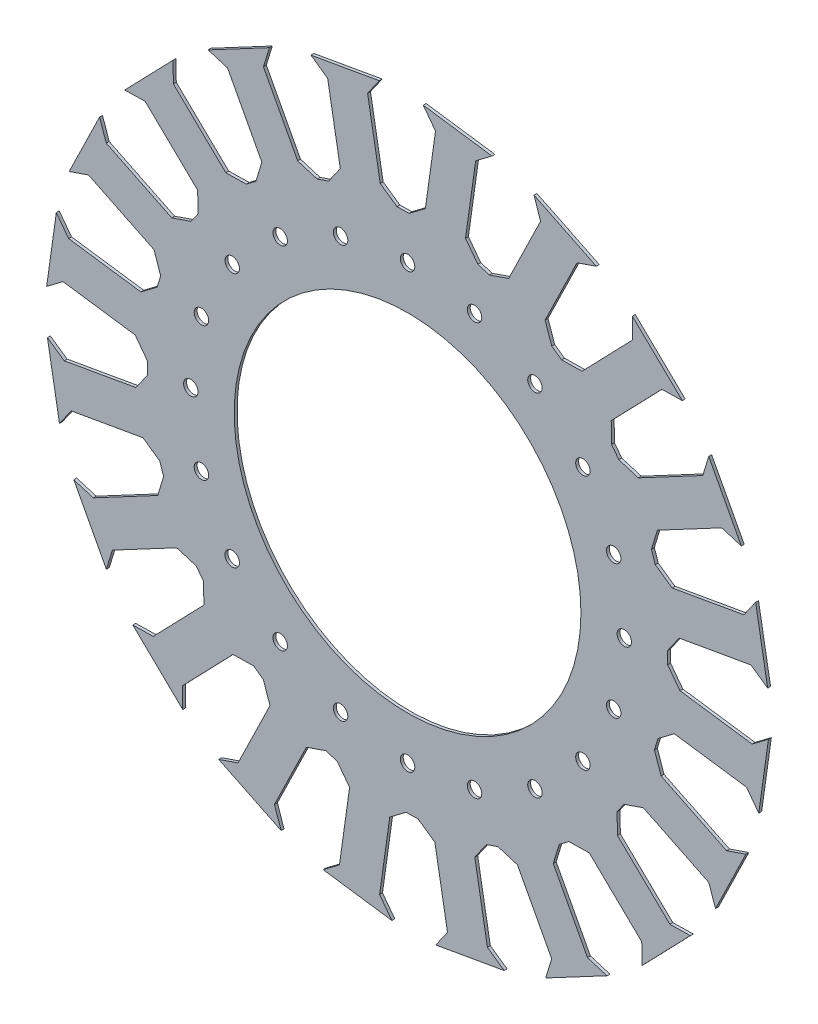
SolidWorks part; units mm, degrees
ref_plane "Ön Düzlem" through (0, 0, 0) normal (0, 0, 1) x (1, 0, 0)
ref_plane "Üst Düzlem" through (0, 0, 0) normal (0, 1, 0) x (1, 0, 0)
ref_plane "Sağ Düzlem" through (0, 0, 0) normal (1, 0, 0) x (0, 0, -1)
sketch "Çizim1" plane through (0, 0, 0) normal (0, 0, 1) x (1, 0, 0)
  line L0 (-3.656, 89.9257) -> (-1.5703, 89.9621)
  line L1 (-27.3209, 85.7529) -> (-29.2933, 85.0738)
  line L2 (-33.438, 120.4446) -> (-9.773, 124.6174)
  line L3 (-9.4482, 93.9815) -> (-13.8288, 118.8251)
  line L4 (-31.2656, 84.3947) -> (-29.2933, 85.0738)
  line L5 (-52.4829, 73.1133) -> (-54.1488, 71.8579)
  line L6 (-69.0208, 104.2167) -> (-47.8036, 115.4981)
  line L7 (-23.2651, 91.5452) -> (-27.6457, 116.3888)
  line L8 (-9.773, 124.6174) -> (-13.8288, 118.8251)
  line L9 (-33.438, 120.4446) -> (-27.6457, 116.3888)
  line L10 (-23.2651, 91.5452) -> (-27.3209, 85.7529)
  line L11 (-9.4482, 93.9815) -> (-3.656, 89.9257)
  line L12 (24.3115, 86.6542) -> (26.3064, 86.0443)
  line L13 (0.5154, 89.9985) -> (-1.5703, 89.9621)
  line L14 (5.418, 124.8825) -> (29.2142, 121.5382)
  line L15 (20.0561, 92.3014) -> (23.567, 117.2827)
  line L16 (6.1626, 94.254) -> (9.6735, 119.2353)
  line L17 (29.2142, 121.5382) -> (23.567, 117.2827)
  line L18 (5.418, 124.8825) -> (9.6735, 119.2353)
  line L19 (6.1626, 94.254) -> (0.5154, 89.9985)
  line L20 (20.0561, 92.3014) -> (24.3115, 86.6542)
  line L21 (49.8993, 74.9004) -> (51.608, 73.7039)
  line L22 (28.3012, 85.4344) -> (26.3064, 86.0443)
  line L23 (43.7437, 117.0961) -> (65.3417, 106.562)
  line L24 (47.5972, 81.5862) -> (58.6559, 104.2599)
  line L25 (34.9871, 87.7365) -> (46.0458, 110.4103)
  line L26 (65.3417, 106.562) -> (58.6559, 104.2599)
  line L27 (43.7437, 117.0961) -> (46.0458, 110.4103)
  line L28 (34.9871, 87.7365) -> (28.3012, 85.4344)
  line L29 (47.5972, 81.5862) -> (49.8993, 74.9004)
  line L30 (70.6025, 55.8147) -> (71.8579, 54.1488)
  line L31 (53.3168, 72.5074) -> (51.608, 73.7039)
  line L32 (77.7874, 97.8475) -> (95.0731, 81.1548)
  line L33 (70.4791, 62.8847) -> (88.0031, 81.0314)
  line L34 (60.3867, 72.6308) -> (77.9108, 90.7775)
  line L35 (95.0731, 81.1548) -> (88.0031, 81.0314)
  line L36 (77.7874, 97.8475) -> (77.9108, 90.7775)
  line L37 (60.3867, 72.6308) -> (53.3168, 72.5074)
  line L38 (70.4791, 62.8847) -> (70.6025, 55.8147)
  line L39 (84.3947, 31.2656) -> (85.0738, 29.2933)
  line L40 (73.1133, 52.4829) -> (71.8579, 54.1488)
  line L41 (104.2167, 69.0208) -> (115.4981, 47.8036)
  line L42 (86.4621, 38.0277) -> (108.736, 49.871)
  line L43 (79.8754, 50.4155) -> (102.1493, 62.2588)
  line L44 (115.4981, 47.8036) -> (108.736, 49.871)
  line L45 (104.2167, 69.0208) -> (102.1493, 62.2588)
  line L46 (79.8754, 50.4155) -> (73.1133, 52.4829)
  line L47 (86.4621, 38.0277) -> (84.3947, 31.2656)
  line L48 (89.9257, 3.656) -> (89.9621, 1.5703)
  line L49 (85.7529, 27.3209) -> (85.0738, 29.2933)
  line L50 (120.4446, 33.438) -> (124.6174, 9.773)
  line L51 (93.9815, 9.4482) -> (118.8251, 13.8288)
  line L52 (91.5452, 23.2651) -> (116.3888, 27.6457)
  line L53 (124.6174, 9.773) -> (118.8251, 13.8288)
  line L54 (120.4446, 33.438) -> (116.3888, 27.6457)
  line L55 (91.5452, 23.2651) -> (85.7529, 27.3209)
  line L56 (93.9815, 9.4482) -> (89.9257, 3.656)
  line L57 (86.6542, -24.3115) -> (86.0443, -26.3064)
  line L58 (89.9985, -0.5154) -> (89.9621, 1.5703)
  line L59 (124.8825, -5.418) -> (121.5382, -29.2142)
  line L60 (92.3014, -20.0561) -> (117.2827, -23.567)
  line L61 (94.254, -6.1626) -> (119.2353, -9.6735)
  line L62 (121.5382, -29.2142) -> (117.2827, -23.567)
  line L63 (124.8825, -5.418) -> (119.2353, -9.6735)
  line L64 (94.254, -6.1626) -> (89.9985, -0.5154)
  line L65 (92.3014, -20.0561) -> (86.6542, -24.3115)
  line L66 (74.9004, -49.8993) -> (73.7039, -51.608)
  line L67 (85.4344, -28.3012) -> (86.0443, -26.3064)
  line L68 (117.0961, -43.7437) -> (106.562, -65.3417)
  line L69 (81.5862, -47.5972) -> (104.2599, -58.6559)
  line L70 (87.7365, -34.9871) -> (110.4103, -46.0458)
  line L71 (106.562, -65.3417) -> (104.2599, -58.6559)
  line L72 (117.0961, -43.7437) -> (110.4103, -46.0458)
  line L73 (87.7365, -34.9871) -> (85.4344, -28.3012)
  line L74 (81.5862, -47.5972) -> (74.9004, -49.8993)
  line L75 (55.8147, -70.6025) -> (54.1488, -71.8579)
  line L76 (72.5074, -53.3168) -> (73.7039, -51.608)
  line L77 (97.8475, -77.7874) -> (81.1548, -95.0731)
  line L78 (62.8847, -70.4791) -> (81.0314, -88.0031)
  line L79 (72.6308, -60.3867) -> (90.7775, -77.9108)
  line L80 (-38.0277, 86.4621) -> (-49.871, 108.736)
  line L81 (81.1548, -95.0731) -> (81.0314, -88.0031)
  line L82 (-50.4155, 79.8754) -> (-62.2588, 102.1493)
  line L83 (97.8475, -77.7874) -> (90.7775, -77.9108)
  line L84 (-47.8036, 115.4981) -> (-49.871, 108.736)
  line L85 (-69.0208, 104.2167) -> (-62.2588, 102.1493)
  line L86 (-50.4155, 79.8754) -> (-52.4829, 73.1133)
  line L87 (-38.0277, 86.4621) -> (-31.2656, 84.3947)
  line L88 (72.6308, -60.3867) -> (72.5074, -53.3168)
  line L90 (-52.4829, 73.1133) -> (-69.0208, 104.2167) construction
  line L92 (-31.2656, 84.3947) -> (-47.8036, 115.4981) construction
  line L93 (-62.2588, 102.1493) -> (-49.871, 108.736) construction
  line L94 (-38.0277, 86.4621) -> (-50.4155, 79.8754) construction
  line L96 (-31.2656, 84.3947) -> (-52.4829, 73.1133) construction
  line L105 (62.8847, -70.4791) -> (55.8147, -70.6025)
  line L106 (31.2656, -84.3947) -> (29.2933, -85.0738)
  line L107 (52.4829, -73.1133) -> (54.1488, -71.8579)
  line L108 (69.0208, -104.2167) -> (47.8036, -115.4981)
  line L109 (38.0277, -86.4621) -> (49.871, -108.736)
  line L110 (50.4155, -79.8754) -> (62.2588, -102.1493)
  line L111 (47.8036, -115.4981) -> (49.871, -108.736)
  line L112 (69.0208, -104.2167) -> (62.2588, -102.1493)
  line L113 (50.4155, -79.8754) -> (52.4829, -73.1133)
  line L114 (38.0277, -86.4621) -> (31.2656, -84.3947)
  line L115 (3.656, -89.9257) -> (1.5703, -89.9621)
  line L116 (27.3209, -85.7529) -> (29.2933, -85.0738)
  line L117 (33.438, -120.4446) -> (9.773, -124.6174)
  line L118 (9.4482, -93.9815) -> (13.8288, -118.8251)
  line L119 (23.2651, -91.5452) -> (27.6457, -116.3888)
  line L120 (9.773, -124.6174) -> (13.8288, -118.8251)
  line L121 (33.438, -120.4446) -> (27.6457, -116.3888)
  line L122 (23.2651, -91.5452) -> (27.3209, -85.7529)
  line L123 (9.4482, -93.9815) -> (3.656, -89.9257)
  line L124 (-24.3115, -86.6542) -> (-26.3064, -86.0443)
  line L125 (-0.5154, -89.9985) -> (1.5703, -89.9621)
  line L126 (-5.418, -124.8825) -> (-29.2142, -121.5382)
  line L127 (-20.0561, -92.3014) -> (-23.567, -117.2827)
  line L128 (-6.1626, -94.254) -> (-9.6735, -119.2353)
  line L129 (-29.2142, -121.5382) -> (-23.567, -117.2827)
  line L130 (-5.418, -124.8825) -> (-9.6735, -119.2353)
  line L131 (-6.1626, -94.254) -> (-0.5154, -89.9985)
  line L132 (-20.0561, -92.3014) -> (-24.3115, -86.6542)
  line L133 (-49.8993, -74.9004) -> (-51.608, -73.7039)
  line L134 (-28.3012, -85.4344) -> (-26.3064, -86.0443)
  line L135 (-43.7437, -117.0961) -> (-65.3417, -106.562)
  line L136 (-47.5972, -81.5862) -> (-58.6559, -104.2599)
  line L137 (-34.9871, -87.7365) -> (-46.0458, -110.4103)
  line L138 (-65.3417, -106.562) -> (-58.6559, -104.2599)
  line L139 (-43.7437, -117.0961) -> (-46.0458, -110.4103)
  line L140 (-34.9871, -87.7365) -> (-28.3012, -85.4344)
  line L141 (-47.5972, -81.5862) -> (-49.8993, -74.9004)
  line L142 (-70.6025, -55.8147) -> (-71.8579, -54.1488)
  line L143 (-53.3168, -72.5074) -> (-51.608, -73.7039)
  line L144 (-77.7874, -97.8475) -> (-95.0731, -81.1548)
  line L145 (-70.4791, -62.8847) -> (-88.0031, -81.0314)
  line L146 (-60.3867, -72.6308) -> (-77.9108, -90.7775)
  line L147 (-95.0731, -81.1548) -> (-88.0031, -81.0314)
  line L148 (-77.7874, -97.8475) -> (-77.9108, -90.7775)
  line L149 (-60.3867, -72.6308) -> (-53.3168, -72.5074)
  line L150 (-70.4791, -62.8847) -> (-70.6025, -55.8147)
  line L151 (-84.3947, -31.2656) -> (-85.0738, -29.2933)
  line L152 (-73.1133, -52.4829) -> (-71.8579, -54.1488)
  line L153 (-104.2167, -69.0208) -> (-115.4981, -47.8036)
  line L154 (-86.4621, -38.0277) -> (-108.736, -49.871)
  line L155 (-79.8754, -50.4155) -> (-102.1493, -62.2588)
  line L156 (-115.4981, -47.8036) -> (-108.736, -49.871)
  line L157 (-104.2167, -69.0208) -> (-102.1493, -62.2588)
  line L158 (-79.8754, -50.4155) -> (-73.1133, -52.4829)
  line L159 (-86.4621, -38.0277) -> (-84.3947, -31.2656)
  line L160 (-89.9257, -3.656) -> (-89.9621, -1.5703)
  line L161 (-85.7529, -27.3209) -> (-85.0738, -29.2933)
  line L162 (-120.4446, -33.438) -> (-124.6174, -9.773)
  line L163 (-93.9815, -9.4482) -> (-118.8251, -13.8288)
  line L164 (-91.5452, -23.2651) -> (-116.3888, -27.6457)
  line L165 (-124.6174, -9.773) -> (-118.8251, -13.8288)
  line L166 (-120.4446, -33.438) -> (-116.3888, -27.6457)
  line L167 (-91.5452, -23.2651) -> (-85.7529, -27.3209)
  line L168 (-93.9815, -9.4482) -> (-89.9257, -3.656)
  line L169 (-86.6542, 24.3115) -> (-86.0443, 26.3064)
  line L170 (-89.9985, 0.5154) -> (-89.9621, -1.5703)
  line L171 (-124.8825, 5.418) -> (-121.5382, 29.2142)
  line L172 (-92.3014, 20.0561) -> (-117.2827, 23.567)
  line L173 (-94.254, 6.1626) -> (-119.2353, 9.6735)
  line L174 (-121.5382, 29.2142) -> (-117.2827, 23.567)
  line L175 (-124.8825, 5.418) -> (-119.2353, 9.6735)
  line L176 (-94.254, 6.1626) -> (-89.9985, 0.5154)
  line L177 (-92.3014, 20.0561) -> (-86.6542, 24.3115)
  line L178 (-74.9004, 49.8993) -> (-73.7039, 51.608)
  line L179 (-85.4344, 28.3012) -> (-86.0443, 26.3064)
  line L180 (-117.0961, 43.7437) -> (-106.562, 65.3417)
  line L181 (-81.5862, 47.5972) -> (-104.2599, 58.6559)
  line L182 (-87.7365, 34.9871) -> (-110.4103, 46.0458)
  line L183 (-106.562, 65.3417) -> (-104.2599, 58.6559)
  line L184 (-117.0961, 43.7437) -> (-110.4103, 46.0458)
  line L185 (-87.7365, 34.9871) -> (-85.4344, 28.3012)
  line L186 (-81.5862, 47.5972) -> (-74.9004, 49.8993)
  line L187 (-55.8147, 70.6025) -> (-54.1488, 71.8579)
  line L188 (-72.5074, 53.3168) -> (-73.7039, 51.608)
  line L189 (-97.8475, 77.7874) -> (-81.1548, 95.0731)
  line L190 (-62.8847, 70.4791) -> (-81.0314, 88.0031)
  line L191 (-72.6308, 60.3867) -> (-90.7775, 77.9108)
  line L192 (-81.1548, 95.0731) -> (-81.0314, 88.0031)
  line L193 (-97.8475, 77.7874) -> (-90.7775, 77.9108)
  line L194 (-72.6308, 60.3867) -> (-72.5074, 53.3168)
  line L195 (-62.8847, 70.4791) -> (-55.8147, 70.6025)
  point P82 (0, 0)
  point P226 (0, 0)
  dimension "D1" = 20
  dimension "D2" = 5
extrude "Yükseklik-Ekstrüzyon1" add sketch "Çizim1" along normal blind 1
sketch "Çizim2" plane through (0, 0, 1) normal (0, 0, 1) x (1, 0, 0)
  circle A0 centre (0, 0) radius 60
extrude "Kes-Ekstrüzyon1" cut sketch "Çizim2" against normal blind 1
sketch "Çizim3" plane through (0, 0, 1) normal (0, 0, 1) x (1, 0, 0)
  circle A0 centre (37.5, 64.9519) radius 2.5
  circle A1 centre (0, 75) radius 2.5
  circle A2 centre (64.9519, 37.5) radius 2.5
  circle A3 centre (75, 0) radius 2.5
  circle A4 centre (64.9519, -37.5) radius 2.5
  circle A5 centre (37.5, -64.9519) radius 2.5
  circle A6 centre (0, -75) radius 2.5
  circle A7 centre (-37.5, -64.9519) radius 2.5
  circle A8 centre (-64.9519, -37.5) radius 2.5
  circle A9 centre (-75, 0) radius 2.5
  circle A10 centre (-64.9519, 37.5) radius 2.5
  circle A11 centre (-37.5, 64.9519) radius 2.5
  point P28 (0, 0)
  dimension "D1" = 12
extrude "Kes-Ekstrüzyon2" cut sketch "Çizim3" against normal blind 1
sketch "Çizim5" plane through (0, 0, 1) normal (0, 0, 1) x (1, 0, 0)
  circle A0 centre (0, 0) radius 60
  circle A1 centre (0, 0) radius 82.2969
extrude "Yükseklik-Ekstrüzyon4" add sketch "Çizim5" against normal blind 1
sketch "Çizim6" plane through (0, 0, 1) normal (0, 0, 1) x (1, 0, 0)
  line L0 (0, 0) -> (0, 75) construction
  line L1 (0, 0) -> (23.1763, 71.3292) construction
  circle A0 centre (23.1763, 71.3292) radius 2.5
  circle A1 centre (0, 75) radius 2.5
  circle A2 centre (44.0839, 60.6763) radius 2.5
  circle A3 centre (60.6763, 44.0839) radius 2.5
  circle A4 centre (71.3292, 23.1763) radius 2.5
  circle A5 centre (75, 0) radius 2.5
  circle A6 centre (71.3292, -23.1763) radius 2.5
  circle A7 centre (60.6763, -44.0839) radius 2.5
  circle A8 centre (44.0839, -60.6763) radius 2.5
  circle A9 centre (23.1763, -71.3292) radius 2.5
  circle A10 centre (0, -75) radius 2.5
  circle A11 centre (-23.1763, -71.3292) radius 2.5
  circle A12 centre (-44.0839, -60.6763) radius 2.5
  circle A13 centre (-60.6763, -44.0839) radius 2.5
  circle A14 centre (-71.3292, -23.1763) radius 2.5
  circle A15 centre (-75, 0) radius 2.5
  circle A16 centre (-71.3292, 23.1763) radius 2.5
  circle A17 centre (-60.6763, 44.0839) radius 2.5
  circle A18 centre (-44.0839, 60.6763) radius 2.5
  circle A19 centre (-23.1763, 71.3292) radius 2.5
  dimension "D1" = 20
  dimension "D2" = 18
extrude "Kes-Ekstrüzyon3" cut sketch "Çizim6" against normal blind 1
